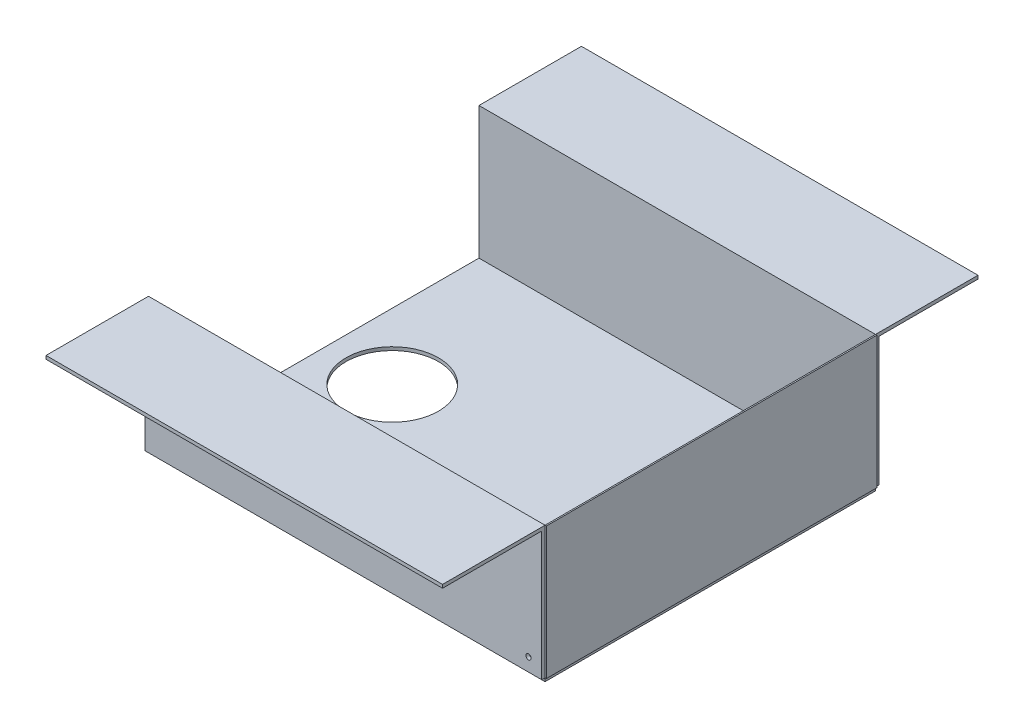
SolidWorks part; units mm, degrees
material "Teak"
ref_plane "Front Plane" through (0, 0, 0) normal (0, 0, 1) x (1, 0, 0)
ref_plane "Top Plane" through (0, 0, 0) normal (0, 1, 0) x (1, 0, 0)
ref_plane "Right Plane" through (0, 0, 0) normal (1, 0, 0) x (0, 0, -1)
sketch "Sketch1" plane through (0, 0, 0) normal (0, 1, 0) x (1, 0, 0)
  line L1 (-137.6667, 116.2429) -> (162.3333, 116.2429)
  line L2 (-137.6667, 116.2429) -> (-137.6667, -133.7571)
  line L3 (-137.6667, -133.7571) -> (162.3333, -133.7571)
  line L4 (162.3333, 116.2429) -> (162.3333, -133.7571)
  dimension "D1" = 250
  dimension "D2" = 300
extrude "Boss-Extrude1" add sketch "Sketch1" along normal blind 2.54
sketch "Sketch2" plane through (0, 2.54, 0) normal (0, 1, 0) x (1, 0, 0)
  line L0 (-137.6667, -133.7571) -> (162.3333, -133.7571) construction
  line L1 (-137.6667, -133.7571) -> (162.3333, -133.7571)
  line L2 (162.3333, 116.2429) -> (-137.6667, 116.2429) construction
  line L3 (162.3333, 116.2429) -> (-137.6667, 116.2429)
extrude "Extrude-Thin1" add sketch "Sketch2" along normal blind 100 separate body thin
sketch "Sketch3" plane through (0, 0, -118.7829) normal (0, 0, -1) x (-1, 0, 0)
  line L0 (-162.3333, 102.54) -> (137.6667, 102.54) construction
  line L1 (-162.3333, 102.54) -> (137.6667, 102.54)
extrude "Extrude-Thin2" add sketch "Sketch3" along normal blind 75 thin
sketch "Sketch4" plane through (0, 0, 136.2971) normal (0, 0, 1) x (1, 0, 0)
  line L0 (-137.6667, 102.54) -> (162.3333, 102.54) construction
  line L1 (-137.6667, 102.54) -> (162.3333, 102.54)
extrude "Extrude-Thin3" add sketch "Sketch4" along normal blind 75 thin
sketch "Sketch5" plane through (0, 0, -118.7829) normal (0, 0, -1) x (-1, 0, 0)
  line L0 (-162.3333, 2.54) -> (137.6667, 2.54) construction
  line L1 (-162.3333, 100) -> (-162.3333, 2.54) construction
  circle A0 centre (-152.3333, 12.54) radius 2
  dimension "D1" = 10
  dimension "D3" = 4
  dimension "D2" = 10
extrude "Cut-Extrude1" cut sketch "Sketch5" against normal through all
sketch "Sketch7" plane through (162.3333, 0, 0) normal (1, 0, 0) x (0, 0, -1)
  line L0 (-133.7571, 2.54) -> (116.2429, 2.54) construction
  line L1 (-133.7571, 2.54) -> (116.2429, 2.54)
  line L2 (116.2429, 102.54) -> (116.2429, 2.54) construction
  line L3 (116.2429, 102.54) -> (116.2429, 2.54)
  line L4 (-133.7571, 102.54) -> (116.2429, 102.54)
  line L6 (-136.2971, 2.54) -> (-133.7571, 2.54)
  line L7 (-133.7571, 2.54) -> (-133.7571, 102.54)
  line L8 (-133.7571, 102.54) -> (-211.2971, 102.54)
  line L9 (-211.2971, 102.54) -> (-211.2971, 100)
  line L10 (-211.2971, 100) -> (-136.2971, 100)
  line L11 (-136.2971, 100) -> (-136.2971, 2.54)
  line L12 (-136.2971, 2.54) -> (-133.7571, 2.54)
  line L13 (-133.7571, 2.54) -> (-133.7571, 102.54)
  line L14 (-133.7571, 102.54) -> (-211.2971, 102.54)
  line L15 (-211.2971, 102.54) -> (-211.2971, 100)
  line L16 (-211.2971, 100) -> (-136.2971, 100)
  line L17 (-136.2971, 100) -> (-136.2971, 2.54)
  line M8 (-133.7571, 2.54) -> (-133.7571, 102.54)
  dimension "D1" = 0
extrude "Boss-Extrude2" add sketch "Sketch7" along normal blind 1 separate body contours L4 L1 L3 M8
sketch "Sketch8" plane through (0, 2.54, 0) normal (0, 1, 0) x (1, 0, 0)
  line L0 (-137.6667, 116.2429) -> (-137.6667, -133.7571) construction
  circle A0 centre (-87.6667, 0.6532) radius 35
  dimension "D1" = 50
extrude "Cut-Extrude2" cut sketch "Sketch8" against normal through all and the other way through all
